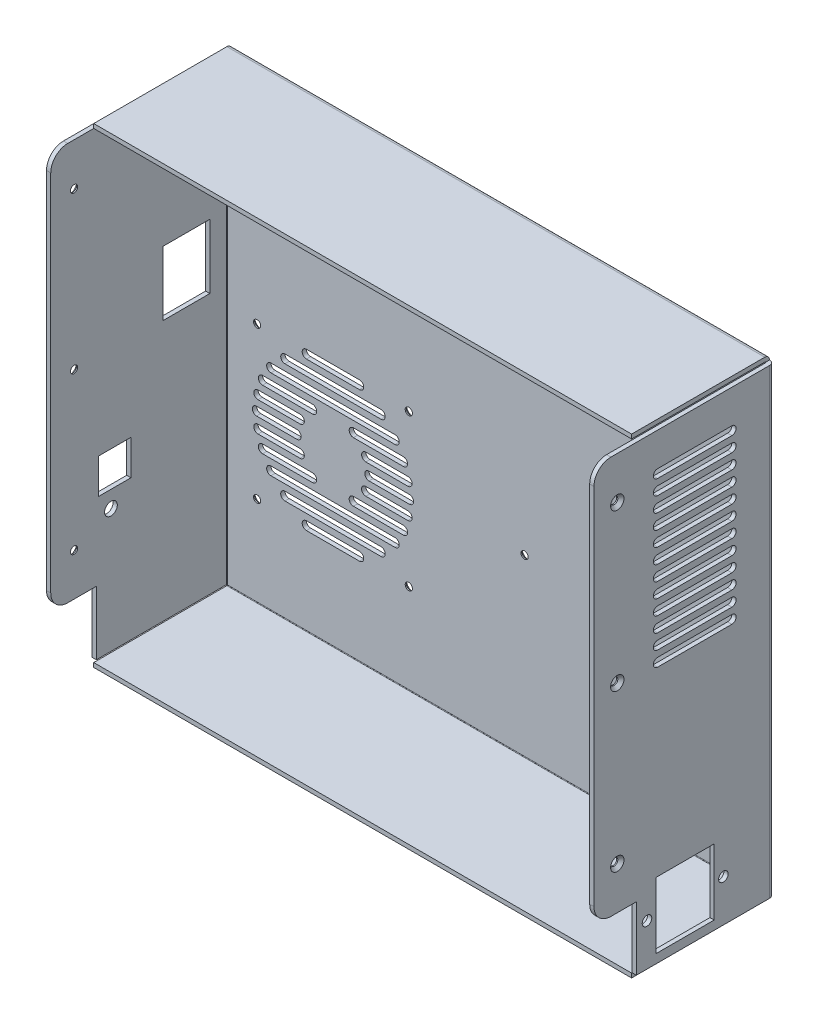
SolidWorks part; units mm, degrees
material "6061-T6 (SS)"
ref_plane "Front Plane" through (0, 0, 0) normal (0, 0, 1) x (1, 0, 0)
ref_plane "Top Plane" through (0, 0, 0) normal (0, 1, 0) x (1, 0, 0)
ref_plane "Right Plane" through (0, 0, 0) normal (1, 0, 0) x (0, 0, -1)
sketch "Sketch1" plane through (0, 0, 0) normal (0, 0, 1) x (1, 0, 0)
  line L0 (-129, 111) -> (129, -111) construction
  line L1 (-129, 111) -> (129, 111)
  line L2 (-129, 111) -> (-129, -111)
  line L3 (-129, -111) -> (129, -111)
  line L4 (129, 111) -> (129, -111)
  dimension "D1" = 258
  dimension "D2" = 222
extrude "Boss-Extrude1" add sketch "Sketch1" along normal blind 2
sketch "Sketch2" plane through (0, 0, 2) normal (0, 0, 1) x (1, 0, 0)
  line L1 (-129, 111) -> (129, 111)
  line L2 (-129, 111) -> (-129, -111)
  line L3 (-129, -111) -> (129, -111)
  line L4 (129, 111) -> (129, -111)
  line L5 (-127, 109) -> (127, 109)
  line L6 (-127, 109) -> (-127, -109)
  line L7 (-127, -109) -> (127, -109)
  line L8 (127, 109) -> (127, -109)
  dimension "D1" = 2
  dimension "D2" = 2
  dimension "D3" = 2
  dimension "D4" = 2
extrude "Boss-Extrude2" add sketch "Sketch2" along normal blind 63
fillet "Fillet1" radius 0.25 4 edges at (0, 109, 2) (127, 0, 2) (0, -109, 2) (-127, 0, 2)
fillet "Fillet2" radius 2.25 4 edges at (0, -111, 0) (129, 0, 0) (0, 111, 0) (-129, 0, 0)
sketch "Sketch3" plane through (0, 0, 65) normal (0, 0, 1) x (1, 0, 0)
  line L0 (-129, -111) -> (129, -111) construction
  line L1 (-126.75, 108.75) -> (-129, 108.75)
  line L2 (-126.75, 108.75) -> (-126.75, 111)
  line L3 (-126.75, 111) -> (-129, 111)
  line L4 (-129, 108.75) -> (-129, 111)
  line L5 (126.75, 108.75) -> (129, 108.75)
  line L6 (126.75, 108.75) -> (126.75, 111)
  line L7 (126.75, 111) -> (129, 111)
  line L8 (129, 108.75) -> (129, 111)
  line L9 (126.75, -108.75) -> (129, -108.75)
  line L10 (126.75, -108.75) -> (126.75, -111)
  line L11 (126.75, -111) -> (129, -111)
  line L12 (129, -108.75) -> (129, -111)
  line L13 (-126.75, -108.75) -> (-129, -108.75)
  line L14 (-126.75, -108.75) -> (-126.75, -111)
  line L15 (-126.75, -111) -> (-129, -111)
  line L16 (-129, -108.75) -> (-129, -111)
extrude "Cut-Extrude1" cut sketch "Sketch3" against normal through all
sketch "Sketch4" plane through (0, 0, 65) normal (0, 0, 1) x (1, 0, 0)
  line L0 (127, -108.75) -> (127, 108.75) construction
  line L1 (129, -108.75) -> (127, -108.75) construction
  line L2 (-127, 108.75) -> (-127, -108.75) construction
  line L3 (-129, 108.75) -> (-127, 108.75)
  line L4 (127, -108.75) -> (129, -108.75)
  line L5 (129, -108.75) -> (129, 108.75)
  line L6 (129, 108.75) -> (127, 108.75)
  line L7 (127, 108.75) -> (127, -108.75)
  line L8 (127, -78.75) -> (129, -78.75)
  line L9 (129, -78.75) -> (129, 108.75)
  line L10 (129, 108.75) -> (127, 108.75)
  line L11 (127, 108.75) -> (127, -78.75)
  line L12 (-129, 108.75) -> (-129, -78.75)
  line L13 (-129, -78.75) -> (-127, -78.75)
  line L14 (-127, 108.75) -> (-127, -78.75)
  dimension "D2" = 30
  dimension "D1" = 0
extrude "Boss-Extrude3" add sketch "Sketch4" along normal blind 20
sketch "Sketch6" plane through (129, 0, 0) normal (1, 0, 0) x (0, 0, -1)
  line L0 (-60, -89) -> (-55.65, -89) construction
  line L1 (-55.65, -73.45) -> (-28.35, -73.45)
  line L2 (-55.65, -73.45) -> (-55.65, -104.55)
  line L3 (-55.65, -104.55) -> (-28.35, -104.55)
  line L4 (-28.35, -73.45) -> (-28.35, -104.55)
  line L5 (-55.65, -89) -> (-28.35, -89) construction
  line L6 (-28.35, -89) -> (-24, -89) construction
  line L8 (-2.25, -111) -> (-65, -111) construction
  line L9 (0, 108.75) -> (0, -108.75) construction
  line L17 (-74, 88.75) -> (-74, 15) construction
  line L18 (-74, 15) -> (-74, -58.75) construction
  line L19 (-85, -78.75) -> (-85, 108.75) construction
  line L20 (-2.25, 108.75) -> (-85, 108.75) construction
  line L21 (-85, -78.75) -> (-65, -78.75) construction
  circle A0 centre (-24, -89) radius 2.25
  circle A1 centre (-60, -89) radius 2.25
  circle A4 centre (-74, -58.75) radius 1.5
  circle A5 centre (-74, 15) radius 1.5
  circle A6 centre (-74, 88.75) radius 1.5
  dimension "D3" = 4.5
  dimension "D10" = 3
  dimension "D1" = 27.3
  dimension "D2" = 36
  dimension "D4" = 31.1
  dimension "D5" = 22
  dimension "D6" = 28.35
  dimension "D11" = 11
  dimension "D12" = 20
  dimension "D13" = 20
extrude "Cut-Extrude3" cut sketch "Sketch6" against normal blind 15
sketch "Sketch5" plane through (-129, 0, 0) normal (-1, 0, 0) x (0, 0, 1)
  line L0 (49.22, -40.6) -> (60.42, -40.6) construction
  line L1 (10, 44.3) -> (32, 44.3)
  line L2 (10, 44.3) -> (10, 14)
  line L3 (10, 14) -> (32, 14)
  line L4 (32, 44.3) -> (32, 14)
  line L5 (47.22, -26.1) -> (62.42, -26.1)
  line L6 (47.22, -26.1) -> (47.22, -42.6)
  line L7 (47.22, -42.6) -> (62.42, -42.6)
  line L8 (62.42, -26.1) -> (62.42, -42.6)
  line L9 (49.22, -40.6) -> (49.22, -28.1) construction
  line L10 (49.22, -28.1) -> (60.42, -28.1) construction
  line L11 (60.42, -40.6) -> (60.42, -28.1) construction
  line L29 (2.25, -111) -> (65, -111) construction
  line L32 (0, -108.75) -> (0, 108.75) construction
  circle A0 centre (74, 88.75) radius 1.5 construction
  circle A1 centre (74, 15) radius 1.5 construction
  circle A2 centre (74, -58.75) radius 1.5 construction
  circle A3 centre (74, 88.75) radius 1.5
  circle A4 centre (74, 15) radius 1.5
  circle A5 centre (74, -58.75) radius 1.5
  circle A6 centre (56.62, -50.5) radius 3
  dimension "D8" = 2
  dimension "D4" = 6
  dimension "D2" = 22
  dimension "D3" = 125
  dimension "D5" = 2
  dimension "D6" = 2
  dimension "D7" = 2
  dimension "D10" = 32
  dimension "D11" = 30.3
extrude "Cut-Extrude2" cut sketch "Sketch5" against normal blind 15
fillet "Fillet3" radius 8 4 edges at (128, -78.75, 85) (128, 108.75, 85) (-128, -78.75, 85) (-128, 108.75, 85)
sketch "Sketch8" plane through (0, 0, 0) normal (0, 0, -1) x (-1, 0, 0)
  line L0 (41.25, 4.75) -> (112.75, -66.75) construction
  line L1 (41, -31) -> (60, -31) construction
  line L2 (41, -29) -> (60, -29)
  line L3 (41, -33) -> (60, -33)
  line L4 (47.7596, -10) -> (106.2404, -10) construction
  line L5 (47.7596, -8) -> (106.2404, -8)
  line L6 (47.7596, -12) -> (106.2404, -12)
  line L7 (43.8338, -17) -> (67.3563, -17) construction
  line L8 (43.8338, -15) -> (67.3563, -15)
  line L9 (43.8338, -19) -> (67.3563, -19)
  line L10 (41.6871, -24) -> (61.5081, -24) construction
  line L11 (41.6871, -22) -> (61.5081, -22)
  line L12 (41.6871, -26) -> (61.5081, -26)
  line L13 (54.3726, -3) -> (99.6274, -3) construction
  line L14 (54.3726, -1) -> (99.6274, -1)
  line L15 (54.3726, -5) -> (99.6274, -5)
  line L16 (64.5, 4) -> (89.5, 4) construction
  line L17 (64.5, 6) -> (89.5, 6)
  line L18 (64.5, 2) -> (89.5, 2)
  line L19 (86.6437, -17) -> (110.1662, -17) construction
  line L20 (86.6437, -15) -> (110.1662, -15)
  line L21 (86.6437, -19) -> (110.1662, -19)
  line L22 (92.4919, -24) -> (112.3129, -24) construction
  line L23 (92.4919, -22) -> (112.3129, -22)
  line L24 (92.4919, -26) -> (112.3129, -26)
  line L25 (94, -31) -> (113, -31) construction
  line L26 (94, -29) -> (113, -29)
  line L27 (94, -33) -> (113, -33)
  line L28 (92.4919, -38) -> (112.3129, -38) construction
  line L29 (92.4919, -36) -> (112.3129, -36)
  line L30 (92.4919, -40) -> (112.3129, -40)
  line L31 (86.6437, -45) -> (110.1662, -45) construction
  line L32 (86.6437, -43) -> (110.1662, -43)
  line L33 (86.6437, -47) -> (110.1662, -47)
  line L34 (41.6871, -38) -> (61.5081, -38) construction
  line L35 (41.6871, -36) -> (61.5081, -36)
  line L36 (41.6871, -40) -> (61.5081, -40)
  line L37 (43.8338, -45) -> (67.3563, -45) construction
  line L38 (43.8338, -43) -> (67.3563, -43)
  line L39 (43.8338, -47) -> (67.3563, -47)
  line L40 (47.7596, -52) -> (106.2404, -52) construction
  line L41 (47.7596, -50) -> (106.2404, -50)
  line L42 (47.7596, -54) -> (106.2404, -54)
  line L43 (54.3726, -59) -> (99.6274, -59) construction
  line L44 (54.3726, -57) -> (99.6274, -57)
  line L45 (54.3726, -61) -> (99.6274, -61)
  line L46 (64.5, -66) -> (89.5, -66) construction
  line L47 (64.5, -64) -> (89.5, -64)
  line L48 (64.5, -68) -> (89.5, -68)
  line L49 (77, -66) -> (77, -59) construction
  line L50 (77, -59) -> (77, -52) construction
  line L51 (77, -52) -> (77, -31) construction
  line L52 (77, -31) -> (77, -10) construction
  line L53 (77, -10) -> (77, -3) construction
  line L54 (77, -3) -> (77, 4) construction
  line L55 (106.2404, -17) -> (106.2404, -24) construction
  line L56 (106.2404, -24) -> (106.2404, -31) construction
  line L57 (106.2404, -31) -> (106.2404, -38) construction
  line L58 (106.2404, -38) -> (106.2404, -45) construction
  line L59 (97.3565, -10) -> (97.3565, -17) construction
  line L60 (99.6274, -45) -> (99.6274, -52) construction
  line L61 (-129, -108.75) -> (-129, 108.75) construction
  line L62 (126.75, -111) -> (-126.75, -111) construction
  circle A0 centre (41.25, 4.75) radius 1.5
  circle A1 centre (41.25, -66.75) radius 1.5
  circle A2 centre (112.75, 4.75) radius 1.5
  circle A3 centre (112.75, -66.75) radius 1.5
  circle A4 centre (77, -31) radius 15 construction
  circle A5 centre (77, -31) radius 38 construction
  arc A6 (41, -29) -> (41, -33) centre (41, -31) ccw
  arc A7 (60, -33) -> (60, -29) centre (60, -31) ccw
  arc A8 (47.7596, -8) -> (47.7596, -12) centre (47.7596, -10) ccw
  arc A9 (106.2404, -12) -> (106.2404, -8) centre (106.2404, -10) ccw
  arc A10 (43.8338, -15) -> (43.8338, -19) centre (43.8338, -17) ccw
  arc A11 (67.3563, -19) -> (67.3563, -15) centre (67.3563, -17) ccw
  arc A12 (41.6871, -22) -> (41.6871, -26) centre (41.6871, -24) ccw
  arc A13 (61.5081, -26) -> (61.5081, -22) centre (61.5081, -24) ccw
  arc A14 (54.3726, -1) -> (54.3726, -5) centre (54.3726, -3) ccw
  arc A15 (99.6274, -5) -> (99.6274, -1) centre (99.6274, -3) ccw
  arc A16 (64.5, 6) -> (64.5, 2) centre (64.5, 4) ccw
  arc A17 (89.5, 2) -> (89.5, 6) centre (89.5, 4) ccw
  arc A18 (86.6437, -15) -> (86.6437, -19) centre (86.6437, -17) ccw
  arc A19 (110.1662, -19) -> (110.1662, -15) centre (110.1662, -17) ccw
  arc A20 (92.4919, -22) -> (92.4919, -26) centre (92.4919, -24) ccw
  arc A21 (112.3129, -26) -> (112.3129, -22) centre (112.3129, -24) ccw
  arc A22 (94, -29) -> (94, -33) centre (94, -31) ccw
  arc A23 (113, -33) -> (113, -29) centre (113, -31) ccw
  arc A24 (92.4919, -36) -> (92.4919, -40) centre (92.4919, -38) ccw
  arc A25 (112.3129, -40) -> (112.3129, -36) centre (112.3129, -38) ccw
  arc A26 (86.6437, -43) -> (86.6437, -47) centre (86.6437, -45) ccw
  arc A27 (110.1662, -47) -> (110.1662, -43) centre (110.1662, -45) ccw
  arc A28 (41.6871, -36) -> (41.6871, -40) centre (41.6871, -38) ccw
  arc A29 (61.5081, -40) -> (61.5081, -36) centre (61.5081, -38) ccw
  arc A30 (43.8338, -43) -> (43.8338, -47) centre (43.8338, -45) ccw
  arc A31 (67.3563, -47) -> (67.3563, -43) centre (67.3563, -45) ccw
  arc A32 (47.7596, -50) -> (47.7596, -54) centre (47.7596, -52) ccw
  arc A33 (106.2404, -54) -> (106.2404, -50) centre (106.2404, -52) ccw
  arc A34 (54.3726, -57) -> (54.3726, -61) centre (54.3726, -59) ccw
  arc A35 (99.6274, -61) -> (99.6274, -57) centre (99.6274, -59) ccw
  arc A36 (64.5, -64) -> (64.5, -68) centre (64.5, -66) ccw
  arc A37 (89.5, -68) -> (89.5, -64) centre (89.5, -66) ccw
  circle A38 centre (-13.3, -26.6) radius 1.5
  circle A39 centre (-93.3, -26.6) radius 1.5
  circle A40 centre (-93.3, 93.4) radius 1.5
  circle A41 centre (-13.3, 93.4) radius 1.5
  circle A42 centre (-67, -96) radius 1.75
  point P17 (50.5, -31)
  point P22 (77, -10)
  point P29 (55.5951, -17)
  point P36 (51.5976, -24)
  point P43 (77, -3)
  point P50 (77, 4)
  point P57 (98.4049, -17)
  point P64 (102.4024, -24)
  point P71 (103.5, -31)
  point P78 (102.4024, -38)
  point P85 (98.4049, -45)
  point P92 (51.5976, -38)
  point P99 (55.5951, -45)
  point P106 (77, -52)
  point P113 (77, -59)
  point P120 (77, -66)
  dimension "D1" = 3
  dimension "D2" = 30
  dimension "D3" = 76
  dimension "D5" = 2
  dimension "D9" = 3.5
  dimension "D4" = 7
  dimension "D6" = 25
  dimension "D7" = 62
  dimension "D8" = 15
extrude "Cut-Extrude5" cut sketch "Sketch8" against normal blind 15
sketch "Sketch10" plane through (0, 0, 65) normal (0, 0, 1) x (1, 0, 0)
  line L4 (-129, -108.75) -> (-127, -108.75)
  line L5 (-127, -108.75) -> (-127, -78.75)
  line L6 (-127, -78.75) -> (-129, -78.75)
  line L7 (-129, -78.75) -> (-129, -108.75)
  line L8 (-129, -108.75) -> (-127, -108.75)
  line L9 (-127, -108.75) -> (-127, -78.75)
  line L10 (-127, -78.75) -> (-129, -78.75)
  line L11 (-129, -78.75) -> (-129, -108.75)
  dimension "D1" = 0
extrude "Cut-Extrude7" cut sketch "Sketch10" against normal blind 1.5
hole_wizard "CSK for M3 Flat Head Machine Screw1" positions "Sketch12" profile "Sketch11" countersink size "M3" standard "Ansi Metric"
sketch "Sketch12" plane through (129, 0, 0) normal (1, 0, 0) x (0, 0, -1)
  point P0 (-74, 88.75)
  point P1 (-74, 15)
  point P4 (-74, -58.75)
sketch "Sketch11" plane through (129, 88.75, 74) normal (0, 1, 0) x (0, 0, -1)
  line L0 (0, 0) -> (0, 11.0215)
  line L1 (0, 11.0215) -> (1.7, 10)
  line L2 (1.7, 10) -> (1.7, 1.45)
  line L3 (1.7, 1.45) -> (3.15, 0)
  line L5 (3.15, 0) -> (0, 0)
  line L6 (-1.7, 1.45) -> (-3.15, 0) construction
  line L10 (0, 11.0215) -> (-1.7, 10) construction
  line L11 (0, -6.35) -> (0, 107.95) construction
  dimension "Hole Dia." = 3.4
  dimension "Hole Depth" = 10
  dimension "Near C'Sink Dia." = 6.3
  dimension "Near C'Sink Angle" = 90
  dimension "Drill Angle" = 118
hole_wizard "CSK for M3 Flat Head Machine Screw2" positions "Sketch14" profile "Sketch13" countersink size "M3" standard "Ansi Metric"
sketch "Sketch14" plane through (-129, 0, 0) normal (-1, 0, 0) x (0, 0, 1)
  point P0 (74, 88.75)
  point P1 (74, 15)
  point P4 (74, -58.75)
sketch "Sketch13" plane through (-129, 88.75, 74) normal (0, 1, 0) x (0, 0, 1)
  line L0 (0, 0) -> (0, 11.0215)
  line L1 (0, 11.0215) -> (1.7, 10)
  line L2 (1.7, 10) -> (1.7, 1.45)
  line L3 (1.7, 1.45) -> (3.15, 0)
  line L5 (3.15, 0) -> (0, 0)
  line L6 (-1.7, 1.45) -> (-3.15, 0) construction
  line L10 (0, 11.0215) -> (-1.7, 10) construction
  line L11 (0, -6.35) -> (0, 107.95) construction
  dimension "Hole Dia." = 3.4
  dimension "Hole Depth" = 10
  dimension "Near C'Sink Dia." = 6.3
  dimension "Near C'Sink Angle" = 90
  dimension "Drill Angle" = 118
hole_wizard "CSK for M3 Flat Head Machine Screw3" positions "Sketch16" profile "Sketch15" countersink size "M3" standard "Ansi Metric"
sketch "Sketch16" plane through (0, 0, 0) normal (0, 0, -1) x (-1, 0, 0)
  point P0 (41.25, 4.75)
  point P1 (112.75, 4.75)
  point P4 (112.75, -66.75)
  point P7 (41.25, -66.75)
  point P13 (-93.3, 93.4)
  point P16 (-13.3, 93.4)
  point P19 (-13.3, -26.6)
  point P22 (-93.3, -26.6)
sketch "Sketch15" plane through (-41.25, 4.75, 0) normal (1, 0, 0) x (0, 1, 0)
  line L0 (0, 0) -> (0, 11.0215)
  line L1 (0, 11.0215) -> (1.7, 10)
  line L2 (1.7, 10) -> (1.7, 1.45)
  line L3 (1.7, 1.45) -> (3.15, 0)
  line L5 (3.15, 0) -> (0, 0)
  line L6 (-1.7, 1.45) -> (-3.15, 0) construction
  line L10 (0, 11.0215) -> (-1.7, 10) construction
  line L11 (0, -6.35) -> (0, 107.95) construction
  dimension "Hole Dia." = 3.4
  dimension "Hole Depth" = 10
  dimension "Near C'Sink Dia." = 6.3
  dimension "Near C'Sink Angle" = 90
  dimension "Drill Angle" = 118
sketch "Sketch17" plane through (129, 0, 0) normal (1, 0, 0) x (0, 0, -1)
  line L0 (-55, 91) -> (-20, 91) construction
  line L1 (-55, 93) -> (-20, 93)
  line L2 (-55, 89) -> (-20, 89)
  line L3 (-2.25, 111) -> (-65, 111) construction
  line L4 (0, 108.75) -> (0, -108.75) construction
  arc A0 (-55, 93) -> (-55, 89) centre (-55, 91) ccw
  arc A1 (-20, 89) -> (-20, 93) centre (-20, 91) ccw
  point P2 (-37.5, 91)
  dimension "D1" = 2
  dimension "D2" = 35
  dimension "D3" = 20
  dimension "D4" = 20
extrude "Cut-Extrude8" cut sketch "Sketch17" against normal blind 10
pattern_linear "LPattern1" count 12 spacing 7 along (0, -1, 0) of "Cut-Extrude8"
